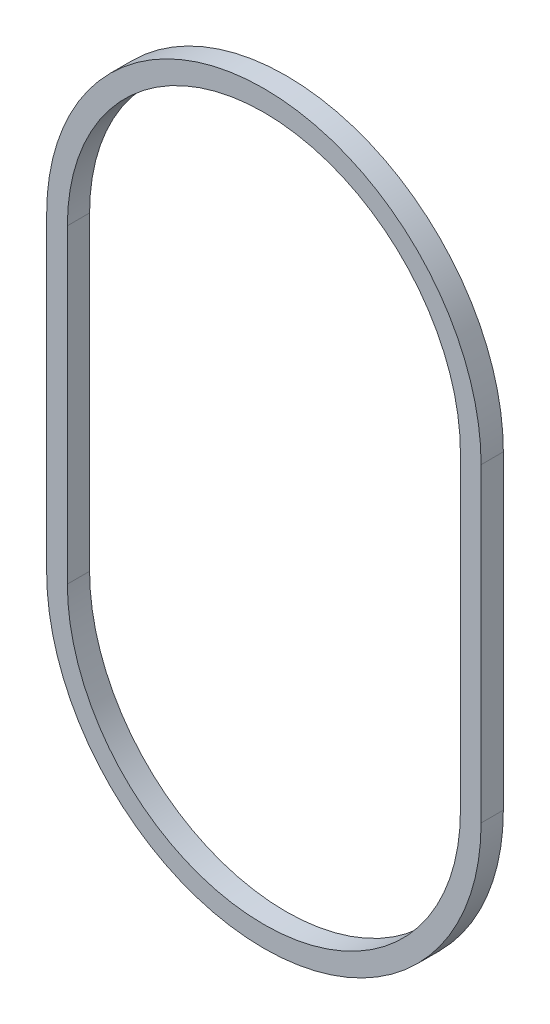
SolidWorks part; units mm, degrees
ref_plane "Front Plane" through (0, 0, 0) normal (0, 0, 1) x (1, 0, 0)
ref_plane "Top Plane" through (0, 0, 0) normal (0, 1, 0) x (1, 0, 0)
ref_plane "Right Plane" through (0, 0, 0) normal (1, 0, 0) x (0, 0, -1)
sketch "Sketch1" plane through (0, 0, 0) normal (0, 0, 1) x (1, 0, 0)
  line L0 (0, -15) -> (0, 15) construction
  line L1 (-20, -15) -> (-20, 15)
  line L2 (20, -15) -> (20, 15)
  arc A0 (-20, -15) -> (20, -15) centre (0, -15) ccw
  arc A1 (20, 15) -> (-20, 15) centre (0, 15) ccw
  point P2 (0, 0)
  dimension "D1" = 40
  dimension "D2" = 30
extrude "Extrude-Thin1" add sketch "Sketch1" along normal mid plane 2.15 thin thin type mid plane wall 2
